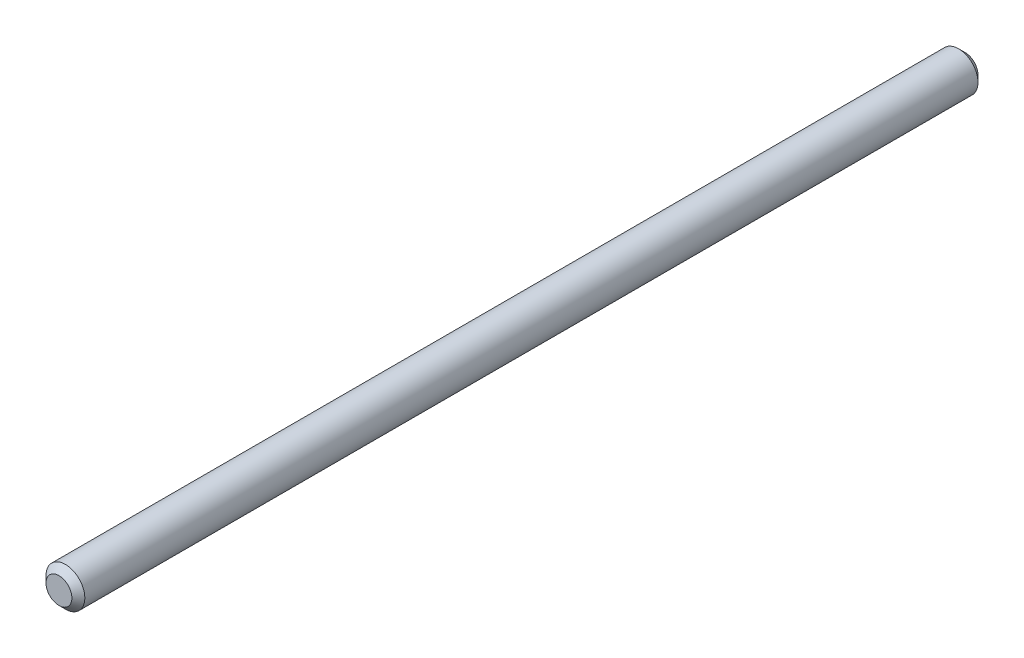
SolidWorks part; units mm, degrees
material "AISI 304"
ref_plane "Front Plane" through (0, 0, 0) normal (0, 0, 1) x (1, 0, 0)
ref_plane "Top Plane" through (0, 0, 0) normal (0, 1, 0) x (1, 0, 0)
ref_plane "Right Plane" through (0, 0, 0) normal (1, 0, 0) x (0, 0, -1)
sketch "Sketch1" plane through (0, 0, 0) normal (0, 0, 1) x (1, 0, 0)
  circle A0 centre (0, 0) radius 1.5
  dimension "D1" = 3
extrude "Boss-Extrude1" add sketch "Sketch1" against normal blind 70
cosmetic thread "Cosmetic Thread1"
chamfer "Chamfer1" distance 0.5 angle 45 2 edges at (1.5, 0, -70) (1.5, 0, 0)
